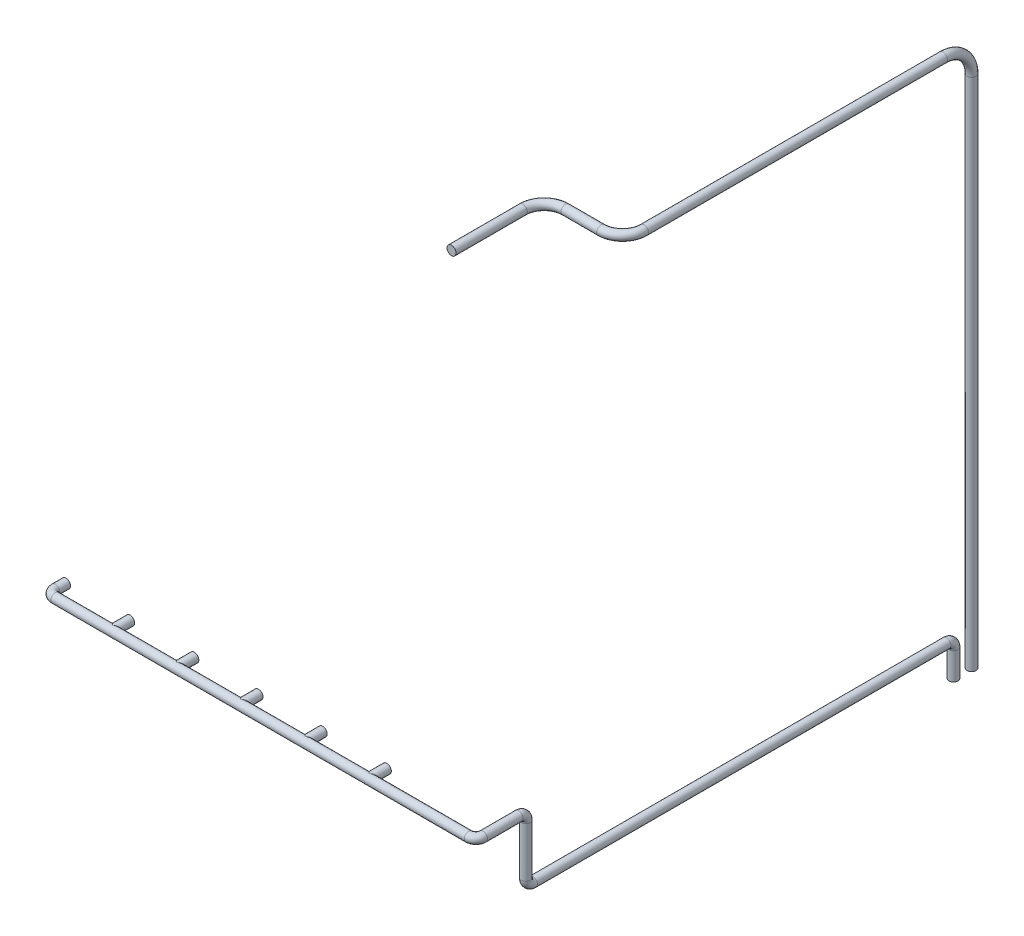
SolidWorks part; units mm, degrees
ref_plane "Alzado" through (0, 0, 0) normal (0, 0, 1) x (1, 0, 0)
ref_plane "Planta" through (0, 0, 0) normal (0, 1, 0) x (1, 0, 0)
ref_plane "Vista lateral" through (0, 0, 0) normal (1, 0, 0) x (0, 0, -1)
sketch "Croquis1" plane through (0, 0, 0) normal (0, 0, 1) x (1, 0, 0)
  circle A0 centre (63.5, 0) radius 63.5
  circle A1 centre (963.5, 0) radius 63.5
  circle A2 centre (1863.5, 0) radius 63.5
  circle A3 centre (2763.5, 0) radius 63.5
  circle A4 centre (3663.5, 0) radius 63.5
  circle A5 centre (4563.5, 0) radius 63.5
  dimension "D1" = 127
  dimension "D2" = 900
  dimension "D3" = 127
  dimension "D4" = 127
  dimension "D5" = 900
  dimension "D6" = 127
  dimension "D7" = 900
  dimension "D8" = 127
  dimension "D9" = 127
  dimension "D10" = 900
  dimension "D11" = 900
extrude "Saliente-Extruir1" add sketch "Croquis1" along normal blind 50
sketch3d "Croquis3D1"
  line L0 (63.5, 0, 50) -> (63.5, 0, 150)
  line L1 (63.5, 0, 50) -> (63.5, 0, 0) construction
  line L2 (163.5, 0, 250) -> (5963.5, 0, 250)
  line L3 (6063.5, 0, 150) -> (6063.5, 0, -350)
  line L4 (6063.5, -100, -450) -> (6063.5, -800, -450)
  line L5 (6063.5, -900, -550) -> (6063.5, -900, -6350)
  line L6 (6063.5, -1000, -6450) -> (6063.5, -1380, -6450)
  arc A0 (6063.5, -900, -6350) -> (6063.5, -1000, -6450) centre (6063.5, -1000, -6350) ccw
  arc A1 (6063.5, -800, -450) -> (6063.5, -900, -550) centre (6063.5, -800, -550) ccw
  arc A2 (6063.5, 0, -350) -> (6063.5, -100, -450) centre (6063.5, -100, -350) ccw
  arc A3 (5963.5, 0, 250) -> (6063.5, 0, 150) centre (5963.5, 0, 150) ccw
  arc A4 (63.5, 0, 150) -> (163.5, 0, 250) centre (163.5, 0, 150) ccw
  point P11 (6063.5, -900, -6450)
  point P12 (5963.5, -1000, -6350)
  point P15 (6063.5, -900, -450)
  point P16 (6163.5, -800, -550)
  point P19 (6063.5, 0, -450)
  point P20 (5963.5, -100, -350)
  point P23 (6063.5, 0, 250)
  point P24 (5963.5, 100, 150)
  point P27 (63.5, 0, 250)
  point P28 (163.5, 100, 150)
  dimension "D7" = 100
  dimension "D1" = 200
  dimension "D2" = 6000
  dimension "D3" = 700
  dimension "D4" = 900
  dimension "D5" = 6000
  dimension "D6" = 480
sketch "Croquis2" plane through (0, 0, 50) normal (0, 0, 1) x (1, 0, 0)
  circle A0 centre (63.5, 0) radius 63.5
sweep "Barrer1" add profiles "Croquis2" path "Croquis3D1"
sketch "Croquis3" plane through (0, 0, 50) normal (0, 0, 1) x (1, 0, 0)
  circle A0 centre (963.5, 0) radius 63.5
extrude "Saliente-Extruir2" add sketch "Croquis3" along normal up to surface (136.5 mm away)
sketch "Croquis4" plane through (0, 0, 50) normal (0, 0, 1) x (1, 0, 0)
  circle A0 centre (1863.5, 0) radius 63.5
extrude "Saliente-Extruir3" add sketch "Croquis4" along normal up to surface (136.5 mm away)
sketch "Croquis5" plane through (0, 0, 50) normal (0, 0, 1) x (1, 0, 0)
  circle A0 centre (2763.5, 0) radius 63.5
extrude "Saliente-Extruir4" add sketch "Croquis5" along normal up to surface (136.5 mm away)
sketch "Croquis6" plane through (0, 0, 50) normal (0, 0, 1) x (1, 0, 0)
  circle A0 centre (3663.5, 0) radius 63.5
extrude "Saliente-Extruir5" add sketch "Croquis6" along normal up to surface (136.5 mm away)
sketch "Croquis7" plane through (0, 0, 50) normal (0, 0, 1) x (1, 0, 0)
  circle A0 centre (4563.5, 0) radius 63.5
extrude "Saliente-Extruir6" add sketch "Croquis7" along normal up to surface (136.5 mm away)
sketch "Croquis8" plane through (0, -1380, 0) normal (0, -1, 0) x (1, 0, 0)
  circle A0 centre (6063.5, -6704) radius 63.5
  circle A1 centre (6063.5, -6450) radius 63.5 construction
  dimension "D1" = 254
  dimension "D2" = 127
extrude "Saliente-Extruir7" add sketch "Croquis8" against normal blind 100 separate body
sketch3d "Croquis3D2"
  line L0 (6063.5, -1280, -6704) -> (6063.5, 5840, -6704)
  line L1 (6063.5, -1280, -6704) -> (6063.5, -1380, -6704) construction
  line L2 (6063.5, 6240, -6304) -> (6063.5, 6240, -2107.7209)
  line L3 (5763.5, 6240, -1807.7209) -> (5263.5, 6240, -1807.7209)
  line L4 (4963.5, 6240, -1507.7209) -> (4963.5, 6240, -507.7209)
  arc A0 (5263.5, 6240, -1807.7209) -> (4963.5, 6240, -1507.7209) centre (5263.5, 6240, -1507.7209) ccw
  arc A1 (6063.5, 5840, -6704) -> (6063.5, 6240, -6304) centre (6063.5, 5840, -6304) ccw
  arc A2 (6063.5, 6240, -2107.7209) -> (5763.5, 6240, -1807.7209) centre (5763.5, 6240, -2107.7209) ccw
  point P8 (6063.5, 6240, -1404)
  point P12 (6063.5, 6240, -6704)
  point P13 (6463.5, 5840, -6304)
  point P14 (4963.5, 6240, -1807.7209)
  point P15 (5263.5, 6540, -1507.7209)
  point P18 (6063.5, 6240, -1807.7209)
  point P19 (5763.5, 5940, -2107.7209)
  dimension "D4" = 1300
  dimension "D5" = 300
  dimension "D1" = 7520
  dimension "D2" = 5300
  dimension "D3" = 1100
sketch "Croquis9" plane through (0, -1280, 0) normal (0, 1, 0) x (1, 0, 0)
  circle A0 centre (6063.5, 6704) radius 63.5
sweep "Barrer2" add profiles "Croquis9" path "Croquis3D2"
